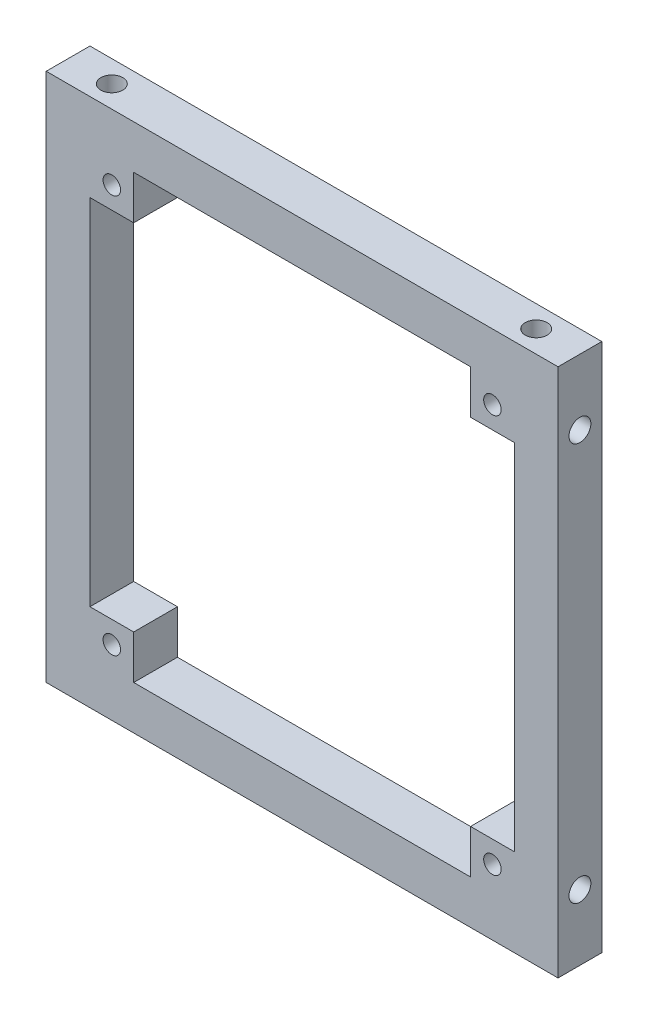
SolidWorks part; units mm, degrees
ref_plane "Front Plane" through (0, 0, 0) normal (0, 0, 1) x (1, 0, 0)
ref_plane "Top Plane" through (0, 0, 0) normal (0, 1, 0) x (1, 0, 0)
ref_plane "Right Plane" through (0, 0, 0) normal (1, 0, 0) x (0, 0, -1)
sketch "Sketch1" plane through (0, 0, 0) normal (0, 0, 1) x (1, 0, 0)
  line L0 (8, 44.4) -> (38.8, 44.4)
  line L1 (0, 48.4) -> (46.8, 48.4)
  line L2 (0, 48.4) -> (0, 0)
  line L3 (0, 0) -> (46.8, 0)
  line L4 (46.8, 48.4) -> (46.8, 0)
  line L5 (42.8, 40.4) -> (42.8, 8)
  line L6 (8, 4) -> (38.8, 4)
  line L7 (4, 40.4) -> (4, 8)
  line L10 (8, 44.4) -> (8, 40.4)
  line L11 (4, 40.4) -> (8, 40.4)
  line L13 (38.8, 44.4) -> (38.8, 40.4)
  line L15 (38.8, 40.4) -> (42.8, 40.4)
  line L16 (38.8, 8) -> (42.8, 8)
  line L17 (38.8, 8) -> (38.8, 4)
  line L20 (4, 8) -> (8, 8)
  line L22 (8, 8) -> (8, 4)
  line L24 (4, 44.4) -> (42.8, 44.4) construction
  line L25 (4, 44.4) -> (4, 4) construction
  line L26 (42.8, 44.4) -> (42.8, 4) construction
  line L27 (42.8, 44.4) -> (42.8, 40.4) [skipped]
  line L28 (4, 4) -> (42.8, 4) construction
  line L29 (42.8, 8) -> (42.8, 4) [skipped]
  line L30 (38.8, 4) -> (42.8, 4) [skipped]
  line L31 (4, 4) -> (8, 4) [skipped]
  circle A1 centre (6, 6) radius 0.8
  circle A2 centre (40.8, 6) radius 0.8
  circle A3 centre (40.8, 42.4) radius 0.8
  circle A4 centre (6, 42.4) radius 0.8
  point P10 (6, 6)
  dimension "D1" = 46.8
  dimension "D2" = 48.4
  dimension "D4" = 4
  dimension "D5" = 4
  dimension "D8" = 8
  dimension "D3" = 4
  dimension "D6" = 2
  dimension "D7" = 2
  dimension "D9" = 2
extrude "left_panel" add sketch "Sketch1" along normal blind 4
sketch "Sketch9" plane through (46.8, 0, 0) normal (1, 0, 0) x (0, 0, -1)
  line L0 (-2, 0) -> (-2, 48.4) construction
  line L1 (-4, 0) -> (0, 0) construction
  line L2 (-4, 48.4) -> (0, 48.4) construction
  circle A0 centre (-2, 6) radius 1
  circle A1 centre (-2, 42.4) radius 1
extrude "Cut-Extrude5" cut sketch "Sketch9" against normal blind 4
sketch "Sketch10" plane through (0, 0, 0) normal (-1, 0, 0) x (0, 0, 1)
  line L0 (2, 48.4) -> (2, 0) construction
  line L1 (4, 48.4) -> (0, 48.4) construction
  line L2 (4, 0) -> (0, 0) construction
  circle A0 centre (2, 6) radius 1
  circle A1 centre (2, 42.4) radius 1
extrude "Cut-Extrude6" cut sketch "Sketch10" against normal blind 4
sketch "Sketch11" plane through (0, 48.4, 0) normal (0, 1, 0) x (1, 0, 0)
  line L0 (0, -2) -> (46.8, -2) construction
  line L1 (0, -4) -> (0, 0) construction
  line L2 (46.8, -4) -> (46.8, 0) construction
  circle A0 centre (4, -2) radius 1
  circle A1 centre (42.8, -2) radius 1
extrude "Cut-Extrude7" cut sketch "Sketch11" against normal blind 4
sketch "Sketch12" plane through (0, 0, 0) normal (0, -1, 0) x (1, 0, 0)
  line L0 (0, 2) -> (46.8, 2) construction
  line L1 (0, 4) -> (0, 0) construction
  line L2 (46.8, 4) -> (46.8, 0) construction
  circle A0 centre (4, 2) radius 1
  circle A1 centre (42.8, 2) radius 1
extrude "Cut-Extrude8" cut sketch "Sketch12" against normal blind 4
equation "\"D1@Sketch1\"=50-3.2"
